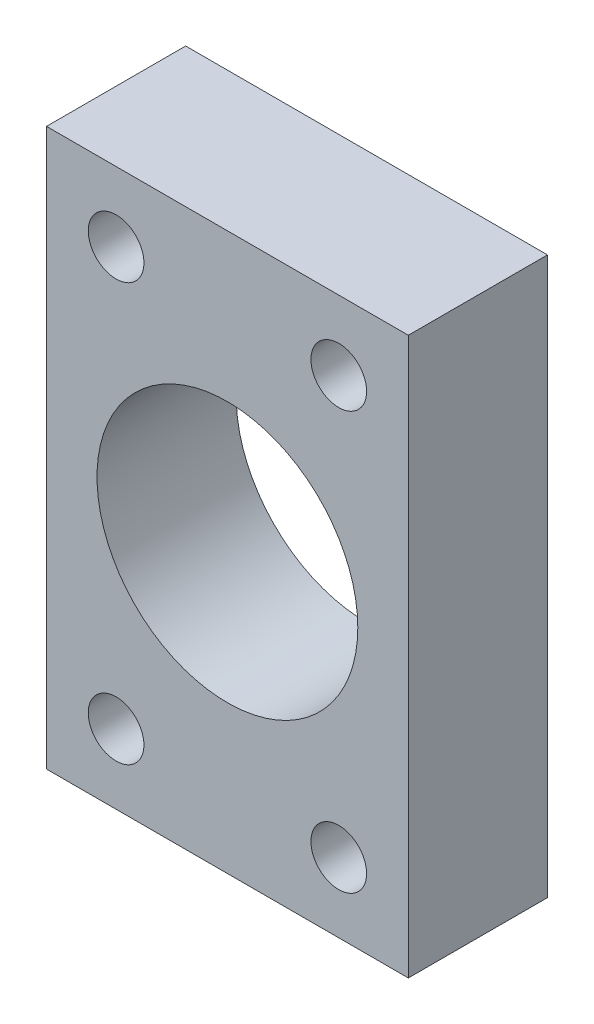
SolidWorks part; units mm, degrees
ref_plane "Front Plane" through (0, 0, 0) normal (0, 0, 1) x (1, 0, 0)
ref_plane "Top Plane" through (0, 0, 0) normal (0, 1, 0) x (1, 0, 0)
ref_plane "Right Plane" through (0, 0, 0) normal (1, 0, 0) x (0, 0, -1)
sketch "Sketch1" plane through (0, 0, 0) normal (0, 0, 1) x (1, 0, 0)
  line L1 (-16.51, 25.4) -> (16.51, 25.4)
  line L2 (-16.51, 25.4) -> (-16.51, -25.4)
  line L3 (-16.51, -25.4) -> (16.51, -25.4)
  line L4 (16.51, 25.4) -> (16.51, -25.4)
  line L5 (-16.51, 25.4) -> (16.51, -25.4) construction
  line L6 (-16.51, -25.4) -> (16.51, 25.4) construction
  line L7 (-10.16, -19.05) -> (10.16, -19.05) construction
  line L8 (-10.16, -19.05) -> (-10.16, 19.05) construction
  line L9 (-10.16, 19.05) -> (10.16, 19.05) construction
  line L10 (10.16, -19.05) -> (10.16, 19.05) construction
  line L11 (-10.16, -19.05) -> (10.16, 19.05) construction
  line L12 (-10.16, 19.05) -> (10.16, -19.05) construction
  circle A0 centre (-10.16, 19.05) radius 2.54
  circle A1 centre (10.16, 19.05) radius 2.54
  circle A2 centre (10.16, -19.05) radius 2.54
  circle A3 centre (-10.16, -19.05) radius 2.54
  circle A4 centre (0, 0) radius 11.8999
  point P0 (0, 0)
  point P6 (0, 0)
  dimension "D1" = 5.08
  dimension "D3" = 23.7998
  dimension "D2" = 20.32
  dimension "D4" = 6.35
  dimension "D5" = 38.1
  dimension "D6" = 6.35
extrude "Boss-Extrude1" add sketch "Sketch1" along normal blind 12.7
